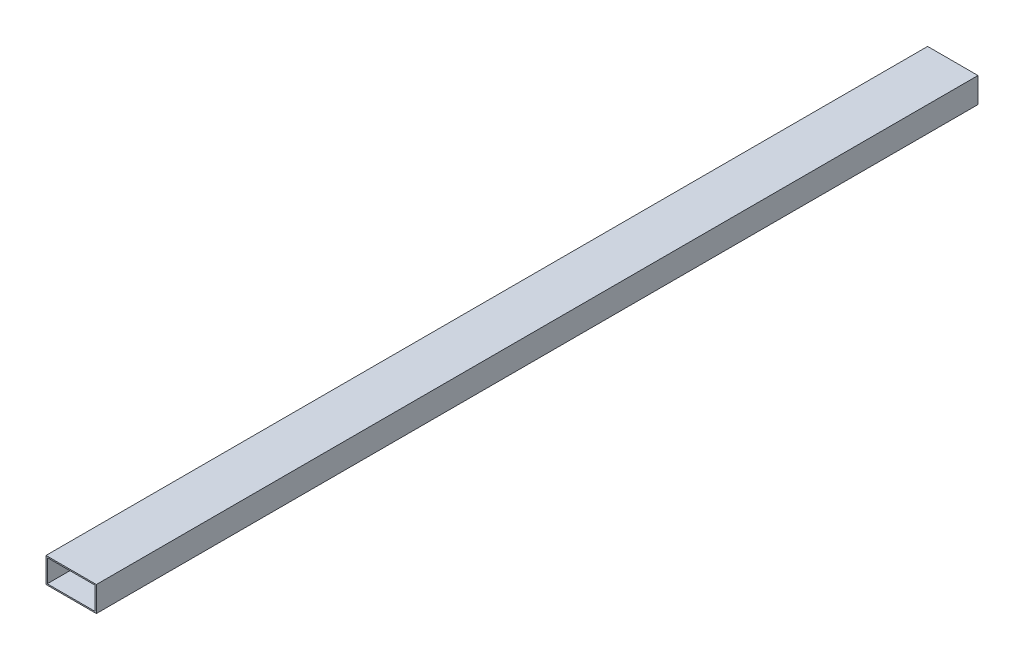
SolidWorks part; units mm, degrees
ref_plane "Front Plane" through (0, 0, 0) normal (0, 0, 1) x (1, 0, 0)
ref_plane "Top Plane" through (0, 0, 0) normal (0, 1, 0) x (1, 0, 0)
ref_plane "Right Plane" through (0, 0, 0) normal (1, 0, 0) x (0, 0, -1)
sketch "Sketch1" plane through (0, 0, 0) normal (0, 0, 1) x (1, 0, 0)
  line L0 (0, 11.6727) -> (0, -12.3549) construction
  line L1 (34.2537, 0) -> (-26.828, 0) construction
  line L2 (-20, 10) -> (20, 10)
  line L3 (20, 10) -> (20, -10)
  line L4 (20, -10) -> (-20, -10)
  line L5 (-20, -10) -> (-20, 10)
  point P7 (-20, 0)
  point P10 (0, -10)
  dimension "D1" = 40
  dimension "D2" = 20
extrude "Boss-Extrude1" add sketch "Sketch1" along normal blind 700
sketch "Sketch2" plane through (0, 0, 700) normal (0, 0, 1) x (1, 0, 0)
  line L18 (-19, 9) -> (-19, -9)
  line L19 (-19, -9) -> (19, -9)
  line L20 (19, -9) -> (19, 9)
  line L21 (19, 9) -> (-19, 9)
  line L22 (-19, 9) -> (-19, -9)
  line L23 (-19, -9) -> (19, -9)
  line L24 (19, -9) -> (19, 9)
  line L25 (19, 9) -> (-19, 9)
  dimension "D1" = 1
extrude "Cut-Extrude1" cut sketch "Sketch2" against normal blind 700
